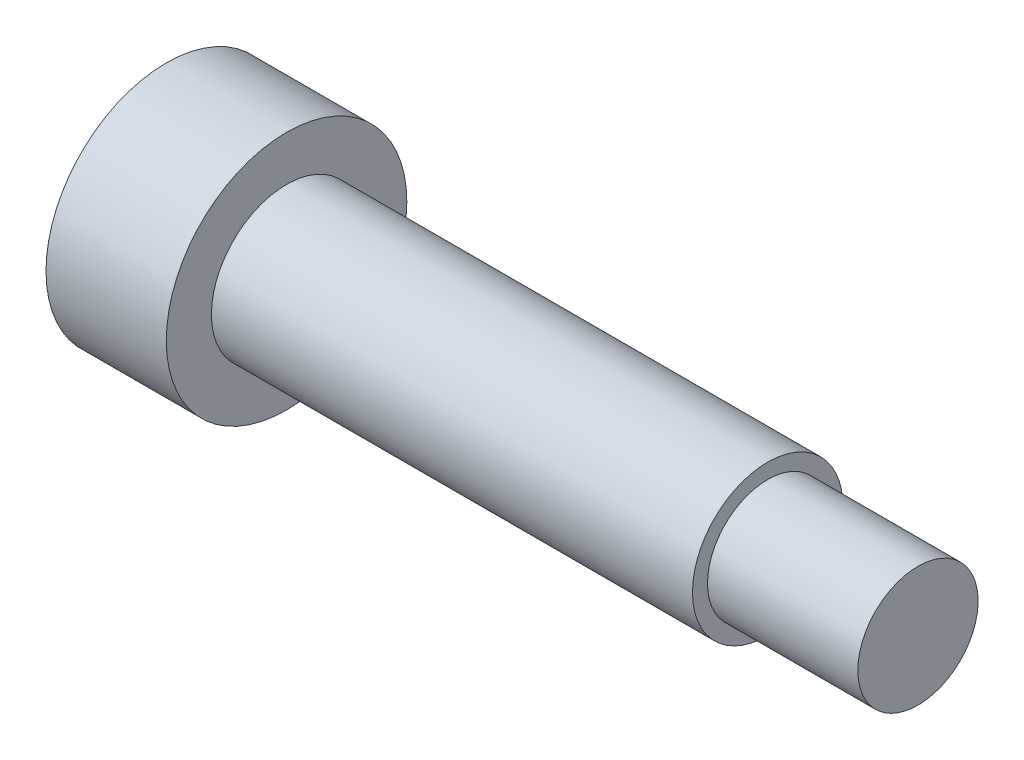
SolidWorks part; units mm, degrees
ref_plane "Front Plane" through (0, 0, 0) normal (0, 0, 1) x (1, 0, 0)
ref_plane "Top Plane" through (0, 0, 0) normal (0, 1, 0) x (1, 0, 0)
ref_plane "Right Plane" through (0, 0, 0) normal (1, 0, 0) x (0, 0, -1)
sketch "Sketch1" plane through (0, 0, 0) normal (0, 0, 1) x (1, 0, 0)
  line L0 (0, 0) -> (25, 0)
  line L1 (25, 0) -> (25, 2)
  line L2 (25, 2) -> (20, 2)
  line L3 (20, 2) -> (20, 2.5)
  line L4 (20, 2.5) -> (4, 2.5)
  line L5 (4, 2.5) -> (4, 4)
  line L6 (4, 4) -> (0, 4)
  line L7 (0, 4) -> (0, 0)
  dimension "D1" = 2.5
  dimension "D2" = 16
  dimension "D3" = 5
  dimension "D4" = 2
  dimension "D5" = 4
  dimension "D6" = 4
revolve "Revolve1" add sketch "Sketch1" angle 360 about L0
sketch "Sketch2" plane through (0, 0, 0) normal (-1, 0, 0) x (0, 0, 1)
  line L1 (-0.2099, 1.428) -> (-1.3417, 0.5322)
  line L2 (-1.3417, 0.5322) -> (-1.1318, -0.8958)
  line L3 (-1.1318, -0.8958) -> (0.2099, -1.428)
  line L4 (0.2099, -1.428) -> (1.3417, -0.5322)
  line L5 (1.3417, -0.5322) -> (1.1318, 0.8958)
  line L6 (1.1318, 0.8958) -> (-0.2099, 1.428)
  circle A0 centre (0, 0) radius 1.25 construction
  dimension "D1" = 2.5
extrude "Cut-Extrude1" cut sketch "Sketch2" against normal blind 1.5
